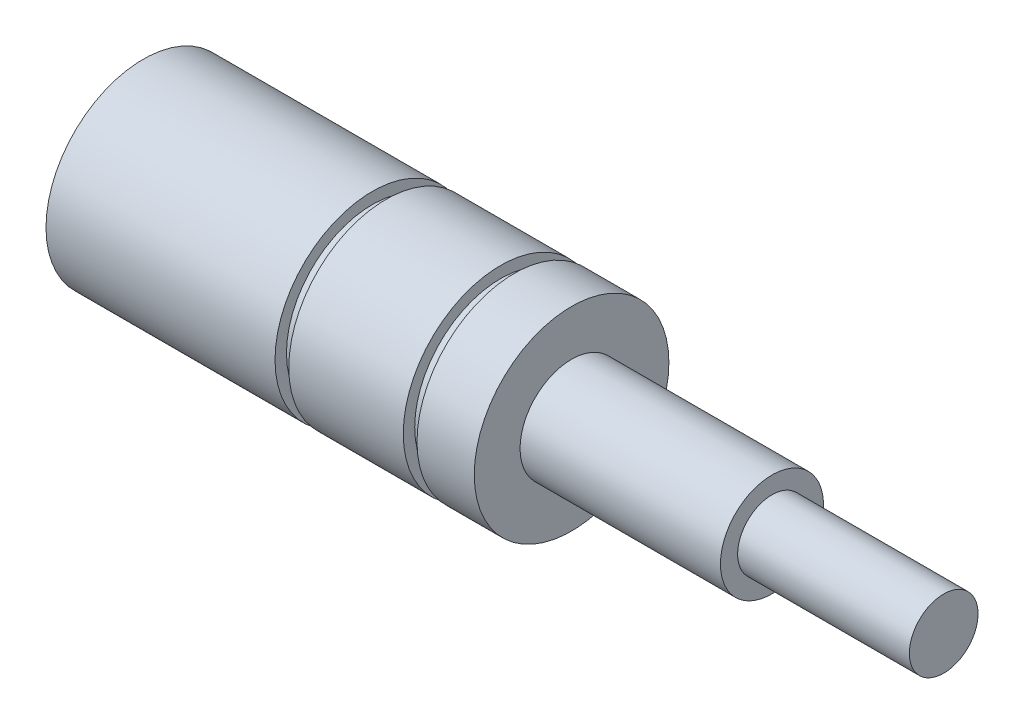
SolidWorks part; units mm, degrees
ref_plane "Front Plane" through (0, 0, 0) normal (0, 0, 1) x (1, 0, 0)
ref_plane "Top Plane" through (0, 0, 0) normal (0, 1, 0) x (1, 0, 0)
ref_plane "Right Plane" through (0, 0, 0) normal (1, 0, 0) x (0, 0, -1)
sketch "Sketch1" plane through (0, 0, 0) normal (0, 0, 1) x (1, 0, 0)
  line L0 (-48.5101, 0) -> (64.7165, 0) construction
  line L1 (-21.4, 4.5) -> (0, 4.5)
  line L2 (0, 4.5) -> (0, 0)
  line L3 (0, 0) -> (48.5, 0)
  line L4 (48.5, 0) -> (48.5, 3)
  line L5 (48.5, 3) -> (33.5, 3)
  line L6 (33.5, 3) -> (33.5, 4.5)
  line L7 (33.5, 4.5) -> (16, 4.5)
  line L8 (16, 4.5) -> (16, 8.5)
  line L9 (16, 8.5) -> (11, 8.5)
  line L10 (11, 8.5) -> (11, 7.5)
  line L11 (11, 7.5) -> (9.8, 7.5)
  line L12 (9.8, 7.5) -> (9.8, 8.5)
  line L13 (9.8, 8.5) -> (-0.2, 8.5)
  line L14 (-0.2, 8.5) -> (-0.2, 7.5)
  line L15 (-0.2, 7.5) -> (-1.4, 7.5)
  line L16 (-1.4, 7.5) -> (-1.4, 8.5)
  line L17 (-1.4, 8.5) -> (-21.4, 8.5)
  line L18 (-21.4, 8.5) -> (-21.4, 4.5)
  point P21 (-0.2, 8)
  dimension "D1" = 20
  dimension "D2" = 10
  dimension "D3" = 5
  dimension "D4" = 17.5
  dimension "D5" = 15
  dimension "D6" = 3
  dimension "D7" = 4.5
  dimension "D8" = 8.5
  dimension "D9" = 1
  dimension "D10" = 1
  dimension "D11" = 1.2
  dimension "D12" = 1.2
  dimension "D13" = 16
revolve "Revolve1" add sketch "Sketch1" angle 360 about L0
